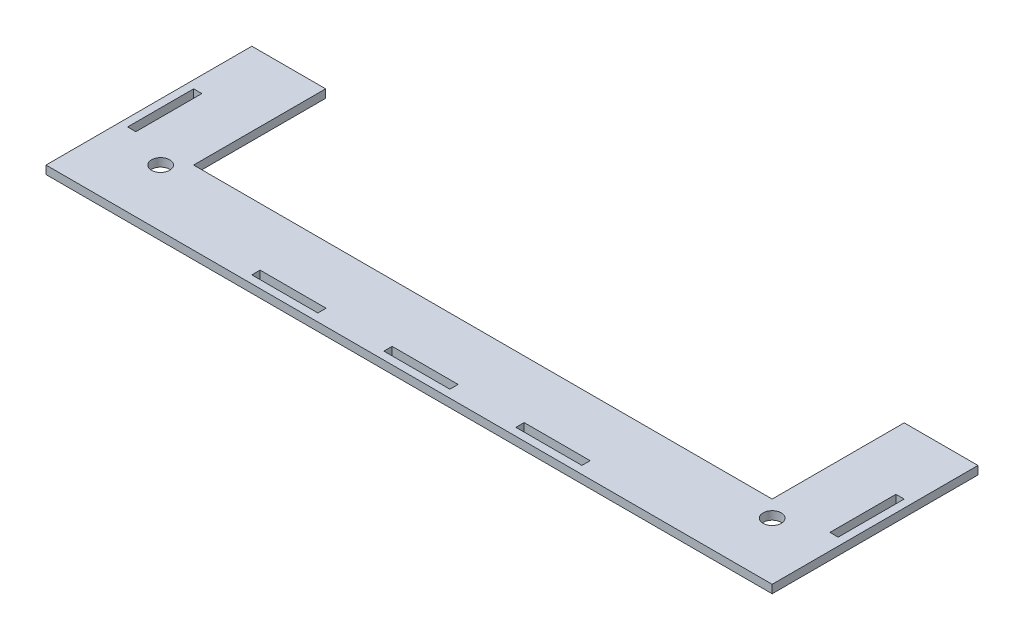
SolidWorks part; units mm, degrees
ref_plane "Front Plane" through (0, 0, 0) normal (0, 0, 1) x (1, 0, 0)
ref_plane "Top Plane" through (0, 0, 0) normal (0, 1, 0) x (1, 0, 0)
ref_plane "Right Plane" through (0, 0, 0) normal (1, 0, 0) x (0, 0, -1)
sketch "Sketch1" plane through (0, 0, 0) normal (0, 1, 0) x (1, 0, 0)
  line L0 (-136.7, 63.5) -> (-111.3, 63.5)
  line L1 (-111.3, 63.5) -> (-111.3, 12.7)
  line L2 (-111.3, 12.7) -> (111.3, 12.7)
  line L3 (111.3, 12.7) -> (111.3, 63.5)
  line L4 (111.3, 63.5) -> (136.7, 63.5)
  line L5 (136.7, 63.5) -> (136.7, -12.7)
  line L6 (136.7, -12.7) -> (-136.7, -12.7)
  line L7 (-136.7, -12.7) -> (-136.7, 63.5)
  line L8 (0, 12.7) -> (0, -12.7) construction
  line L9 (-111.3, 12.7) -> (-111.3, 6.35) construction
  line L10 (-111.3, 6.35) -> (-117.65, 6.35) construction
  line L11 (111.3, 12.7) -> (111.3, 6.35) construction
  line L12 (111.3, 6.35) -> (117.65, 6.35) construction
  line L13 (-38.1, -9.525) -> (-12.7, -9.525) construction
  line L14 (-12.7, -12.7) -> (12.7, -12.7)
  line L15 (-12.7, -12.7) -> (-12.7, -9.525)
  line L16 (-12.7, -9.525) -> (12.7, -9.525)
  line L17 (12.7, -12.7) -> (12.7, -9.525)
  line L18 (38.1, -12.7) -> (63.5, -12.7)
  line L19 (38.1, -12.7) -> (38.1, -9.525)
  line L20 (38.1, -9.525) -> (63.5, -9.525)
  line L21 (63.5, -12.7) -> (63.5, -9.525)
  line L22 (-63.5, -12.7) -> (-38.1, -12.7)
  line L23 (-63.5, -12.7) -> (-63.5, -9.525)
  line L24 (-63.5, -9.525) -> (-38.1, -9.525)
  line L25 (-38.1, -12.7) -> (-38.1, -9.525)
  line L26 (12.7, -9.525) -> (38.1, -9.525) construction
  line L27 (-133.525, 12.7) -> (-133.525, -12.7) construction
  line L28 (-136.7, 12.7) -> (-133.525, 12.7)
  line L29 (-136.7, 12.7) -> (-136.7, 38.1)
  line L30 (-136.7, 38.1) -> (-133.525, 38.1)
  line L31 (-133.525, 12.7) -> (-133.525, 38.1)
  line L32 (136.7, 12.7) -> (133.525, 12.7)
  line L33 (136.7, 12.7) -> (136.7, 38.1)
  line L34 (136.7, 38.1) -> (133.525, 38.1)
  line L35 (133.525, 12.7) -> (133.525, 38.1)
  line L36 (-136.7, 63.5) -> (-139.7, 63.5)
  line L37 (-139.7, 63.5) -> (-139.7, -15.7)
  line L38 (-139.7, -15.7) -> (139.7, -15.7)
  line L39 (139.7, -15.7) -> (139.7, 63.5)
  line L40 (139.7, 63.5) -> (136.7, 63.5)
  line L41 (-136.7, -12.7) -> (-136.7, -15.7) construction
  circle A0 centre (-117.65, 6.35) radius 3.5
  circle A1 centre (117.65, 6.35) radius 3.5
  point P10 (0, 12.7)
  point P11 (0, -12.7)
  point P14 (0, 0)
  point P32 (0, -9.525)
  dimension "D5" = 7
  dimension "D1" = 273.4
  dimension "D2" = 76.2
  dimension "D3" = 25.4
  dimension "D4" = 25.4
  dimension "D6" = 6.35
  dimension "D7" = 25.4
  dimension "D8" = 3.175
  dimension "D9" = 25.4
  dimension "D10" = 3.175
  dimension "D11" = 3
extrude "Boss-Extrude1" add sketch "Sketch1" along normal blind 3.175 contours L25 L6 L15 L16 L17 L19 L20 L21 L5 L4 L3 L2 L1 L0 L7 L23 L24 A1 A0 | L39 L40 L5 L6 L7 L36 L37 L38
